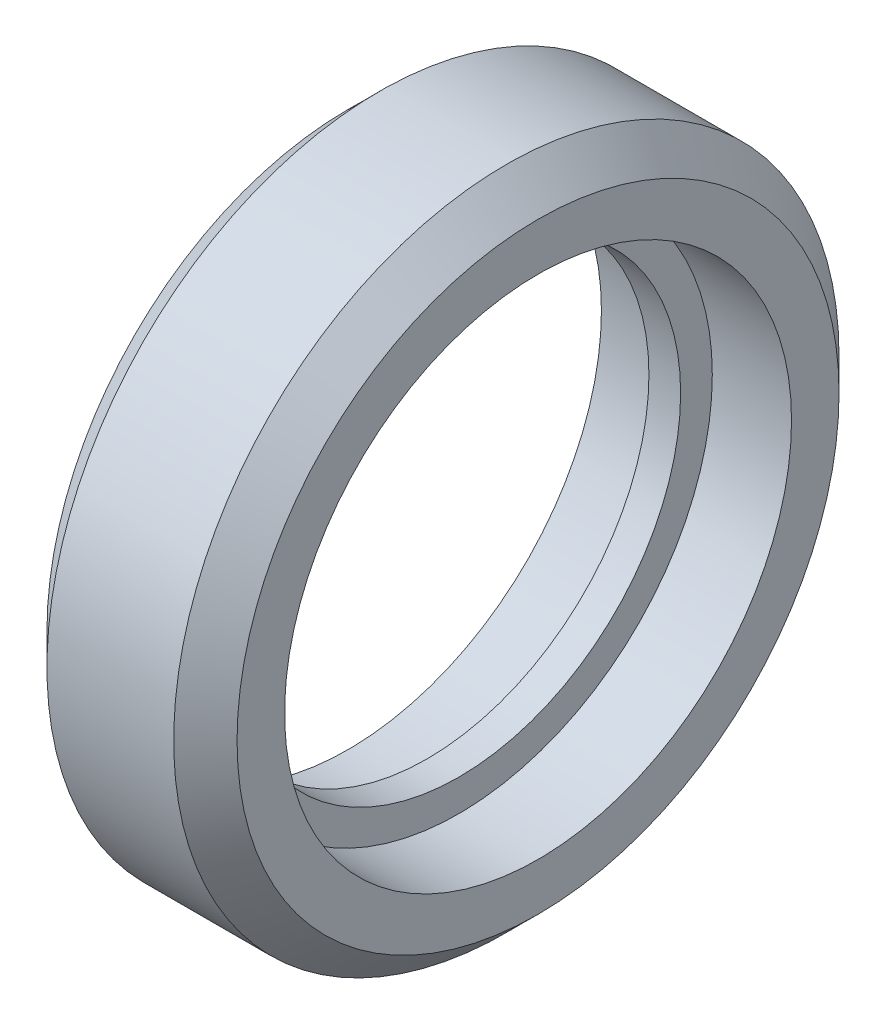
SolidWorks part; units mm, degrees
ref_plane "Front Plane" through (0, 0, 0) normal (0, 0, 1) x (1, 0, 0)
ref_plane "Top Plane" through (0, 0, 0) normal (0, 1, 0) x (1, 0, 0)
ref_plane "Right Plane" through (0, 0, 0) normal (1, 0, 0) x (0, 0, -1)
sketch "Sketch1" plane through (0, 0, 0) normal (0, 0, 1) x (1, 0, 0)
  line L0 (0, 0) -> (0, 8) construction
  line L1 (0, -5.225) -> (0, 5.225) construction
  line L2 (0, 7) -> (-0.5, 7)
  line L3 (-0.5, 7) -> (-0.5, 8)
  line L4 (-0.5, 8) -> (-3, 8)
  line L5 (-3, 8) -> (-3, 9.5)
  line L6 (-3, 9.5) -> (-2, 10.5)
  line L7 (-2, 10.5) -> (0, 10.5)
  line L8 (0, 10.5) -> (0, 7)
  line L9 (4.8638, 0) -> (-4.8638, 0) construction
  line L10 (0, 0) -> (-8.8433, 0) construction
  point P5 (0, 7)
  dimension "D1" = 7
  dimension "D2" = 3
  dimension "D3" = 2
  dimension "D4" = 45
  dimension "D5" = 8
revolve "Revolve1" add sketch "Sketch1" angle 360 about L10
mirror "Mirror1" about plane through (0, 10.5, 0) normal (1, 0, 0) of "Revolve1"
